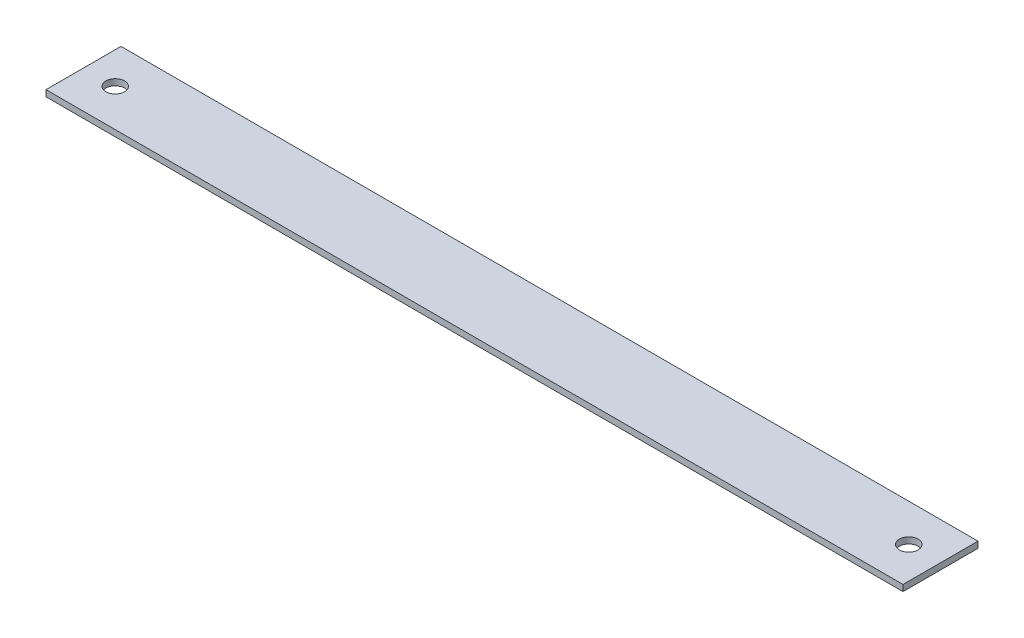
SolidWorks part; units mm, degrees
ref_plane "Front Plane" through (0, 0, 0) normal (0, 0, 1) x (1, 0, 0)
ref_plane "Top Plane" through (0, 0, 0) normal (0, 1, 0) x (1, 0, 0)
ref_plane "Right Plane" through (0, 0, 0) normal (1, 0, 0) x (0, 0, -1)
sketch "Sketch1" plane through (0, 0, 0) normal (0, 1, 0) x (1, 0, 0)
  line L1 (0, 0) -> (685.8, 0)
  line L2 (0, 0) -> (0, 60)
  line L3 (0, 60) -> (685.8, 60)
  line L4 (685.8, 0) -> (685.8, 60)
  circle A0 centre (25.4, 30) radius 7.5
  circle A1 centre (660.4, 30) radius 7.5
  point P10 (685.8, 30)
  dimension "D3" = 15
  dimension "D6" = 15
  dimension "D1" = 685.8
  dimension "D2" = 60
  dimension "D4" = 25.4
  dimension "D5" = 25.4
extrude "Boss-Extrude1" add sketch "Sketch1" along normal blind 5 contours L1 L4 L3 L2 A1 A0
